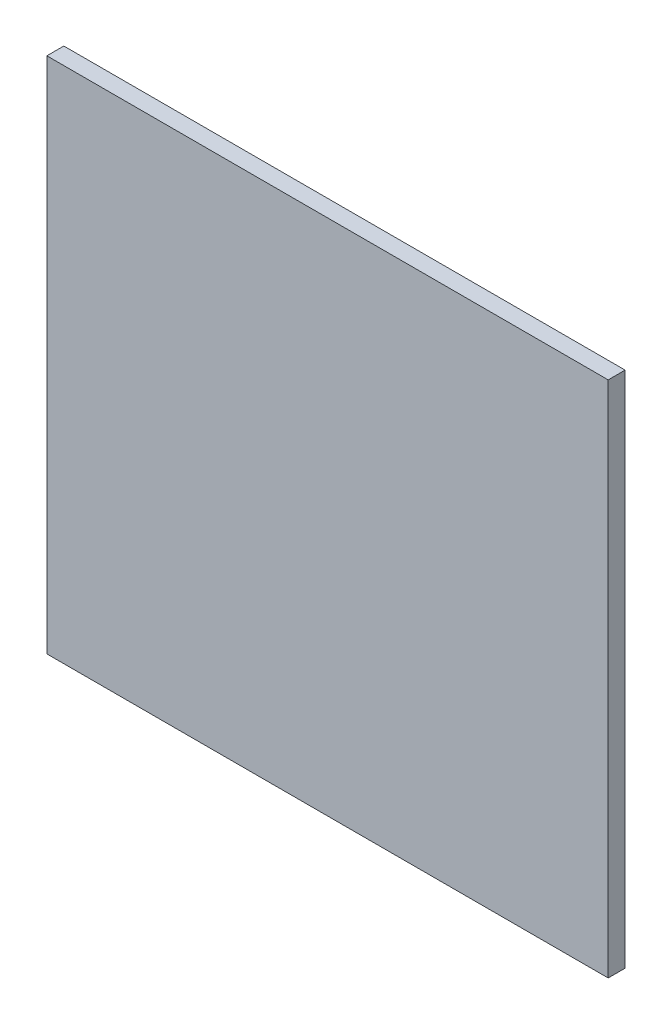
SolidWorks part; units mm, degrees
ref_plane "Front Plane" through (0, 0, 0) normal (0, 0, 1) x (1, 0, 0)
ref_plane "Top Plane" through (0, 0, 0) normal (0, 1, 0) x (1, 0, 0)
ref_plane "Right Plane" through (0, 0, 0) normal (1, 0, 0) x (0, 0, -1)
sketch "Sketch1" plane through (0, 0, 0) normal (0, 0, 1) x (1, 0, 0)
  line L1 (548.2488, -36.5015) -> (-47.7512, -36.5015)
  line L2 (548.2488, -36.5015) -> (548.2488, 513.4985)
  line L3 (548.2488, 513.4985) -> (-47.7512, 513.4985)
  line L4 (-47.7512, -36.5015) -> (-47.7512, 513.4985)
  line L5 (548.2488, -36.5015) -> (-47.7512, 513.4985) construction
  line L6 (548.2488, 513.4985) -> (-47.7512, -36.5015) construction
  point P0 (250.2488, 238.4985)
  dimension "D1" = 550
  dimension "D2" = 596
extrude "Boss-Extrude1" add sketch "Sketch1" along normal blind 18
